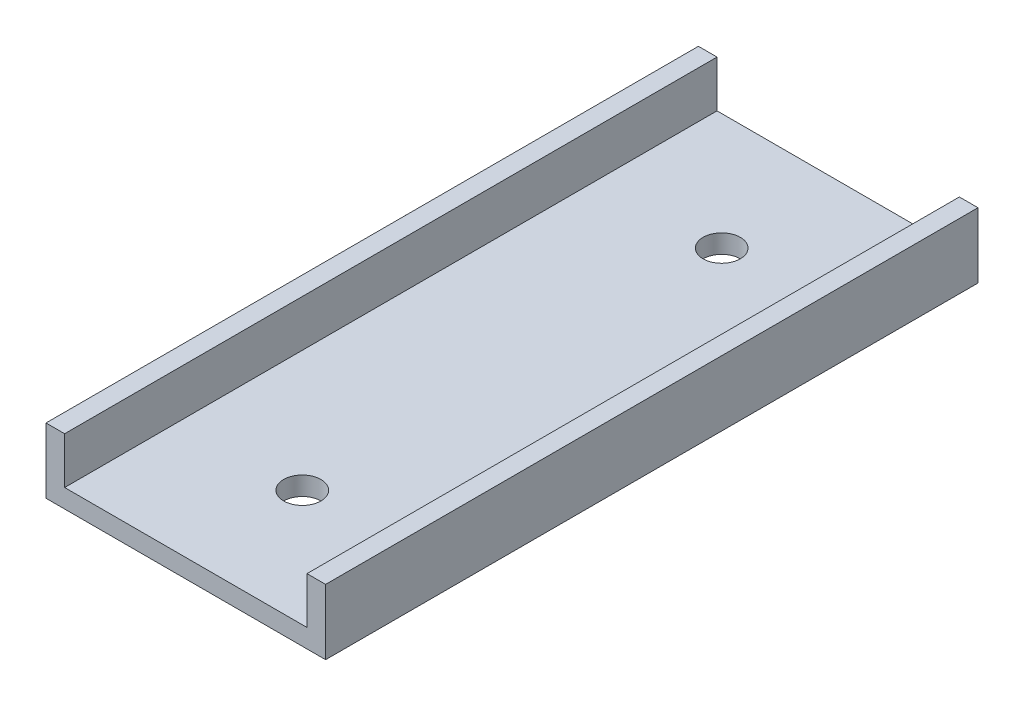
SolidWorks part; units mm, degrees
ref_plane "前视基准面" through (0, 0, 0) normal (0, 0, 1) x (1, 0, 0)
ref_plane "上视基准面" through (0, 0, 0) normal (0, 1, 0) x (1, 0, 0)
ref_plane "右视基准面" through (0, 0, 0) normal (1, 0, 0) x (0, 0, -1)
sketch "草图1" plane through (0, 0, 0) normal (0, 0, 1) x (1, 0, 0)
  line L0 (-39.7391, 13.5785) -> (-39.7391, 6.5785)
  line L1 (-39.7391, 6.5785) -> (-9.7391, 6.5785)
  line L2 (-9.7391, 6.5785) -> (-9.7391, 13.5785)
  line L3 (-9.7391, 13.5785) -> (-11.7391, 13.5785)
  line L4 (-11.7391, 13.5785) -> (-11.7391, 8.5785)
  line L5 (-11.7391, 8.5785) -> (-37.7391, 8.5785)
  line L6 (-37.7391, 8.5785) -> (-37.7391, 13.5785)
  line L7 (-37.7391, 13.5785) -> (-39.7391, 13.5785)
  dimension "D1" = 7
  dimension "D2" = 30
  dimension "D3" = 2
  dimension "D4" = 5
  dimension "D5" = 26
extrude "凸台-拉伸1" add sketch "草图1" along normal blind 70
sketch "草图2" plane through (0, 6.5785, 0) normal (0, -1, 0) x (-1, 0, 0)
  line L0 (24.7391, 0) -> (24.7391, -12.5) construction
  line L1 (39.7391, 0) -> (9.7391, 0) construction
  line L2 (9.7391, -35) -> (39.7391, -35) construction
  line L3 (9.7391, -70) -> (9.7391, 0) construction
  line L4 (39.7391, -70) -> (39.7391, 0) construction
  line L5 (24.7391, -70) -> (24.7391, -57.5) construction
  circle A0 centre (24.7391, -12.5) radius 2
  circle A1 centre (24.7391, -57.5) radius 2
  dimension "D2" = 4
  dimension "D1" = 12.5
extrude "切除-拉伸1" cut sketch "草图2" against normal blind 70
